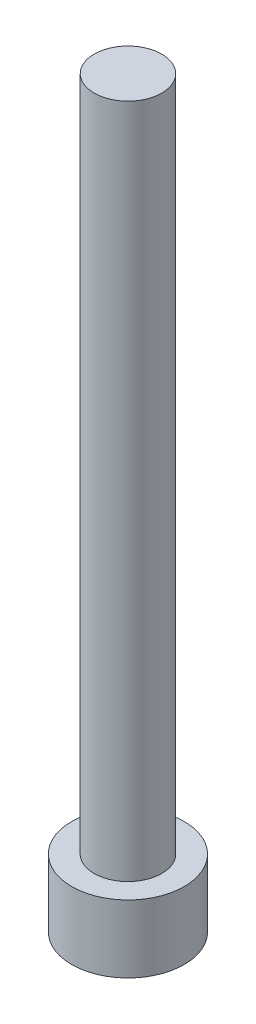
SolidWorks part; units mm, degrees
ref_plane "前视基准面" through (0, 0, 0) normal (0, 0, 1) x (1, 0, 0)
ref_plane "上视基准面" through (0, 0, 0) normal (0, 1, 0) x (1, 0, 0)
ref_plane "右视基准面" through (0, 0, 0) normal (1, 0, 0) x (0, 0, -1)
sketch "草图1" plane through (0, 0, 0) normal (0, 1, 0) x (1, 0, 0)
  circle A0 centre (0, 0) radius 2.5
  dimension "D1" = 5
extrude "凸台-拉伸1" add sketch "草图1" along normal blind 3
sketch "草图2" plane through (0, 3, 0) normal (0, 1, 0) x (1, 0, 0)
  circle A0 centre (0, 0) radius 1.5
extrude "凸台-拉伸2" add sketch "草图2" along normal blind 30
sketch "草图3" plane through (0, 0, 0) normal (0, -1, 0) x (1, 0, 0)
  line L1 (1.425, 0) -> (0.7125, 1.2341)
  line L2 (0.7125, 1.2341) -> (-0.7125, 1.2341)
  line L3 (-0.7125, 1.2341) -> (-1.425, 0)
  line L4 (-1.425, 0) -> (-0.7125, -1.2341)
  line L5 (-0.7125, -1.2341) -> (0.7125, -1.2341)
  line L6 (0.7125, -1.2341) -> (1.425, 0)
  circle A0 centre (0, 0) radius 1.2341 construction
extrude "切除-拉伸1" cut sketch "草图3" against normal blind 1.65
